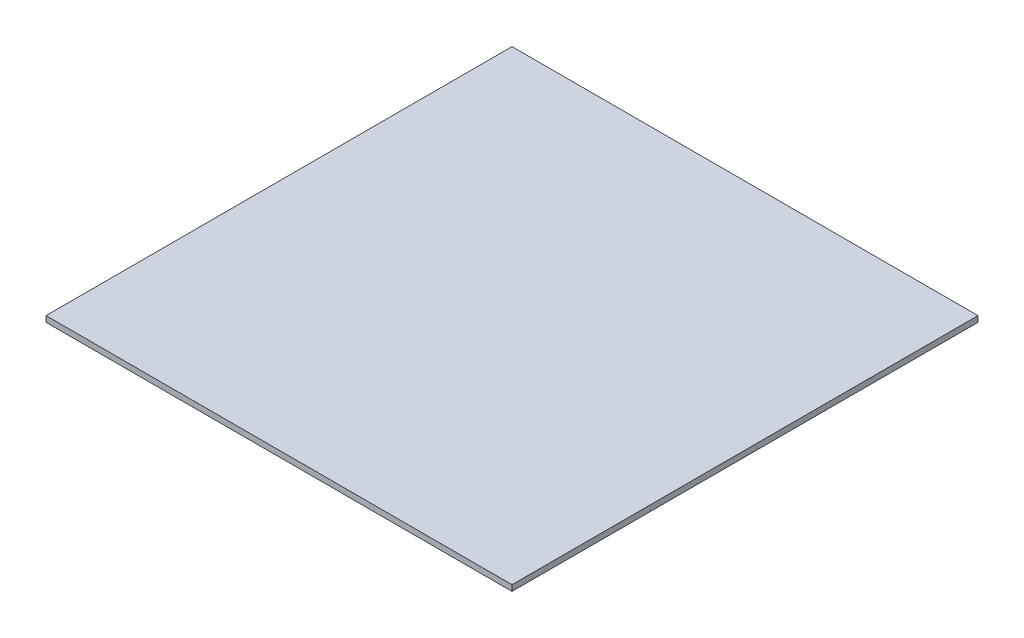
SolidWorks part; units mm, degrees
ref_plane "Front Plane" through (0, 0, 0) normal (0, 0, 1) x (1, 0, 0)
ref_plane "Top Plane" through (0, 0, 0) normal (0, 1, 0) x (1, 0, 0)
ref_plane "Right Plane" through (0, 0, 0) normal (1, 0, 0) x (0, 0, -1)
sketch "Sketch1" plane through (0, 0, 0) normal (0, 1, 0) x (1, 0, 0)
  line L1 (-306.2808, 448.1854) -> (493.7192, 448.1854)
  line L2 (-306.2808, 448.1854) -> (-306.2808, -351.8146)
  line L3 (-306.2808, -351.8146) -> (493.7192, -351.8146)
  line L4 (493.7192, 448.1854) -> (493.7192, -351.8146)
  dimension "D1" = 800
  dimension "D2" = 800
extrude "Boss-Extrude1" add sketch "Sketch1" along normal blind 10
